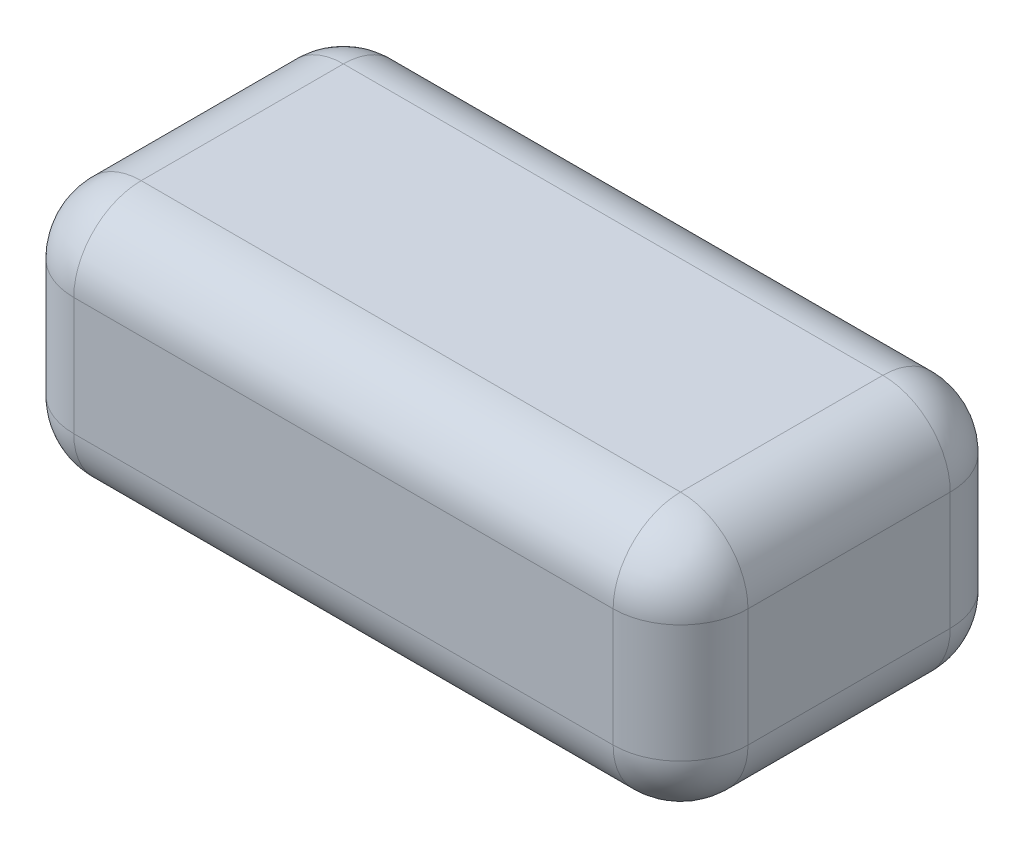
SolidWorks part; units mm, degrees
ref_plane "Front Plane" through (0, 0, 0) normal (0, 0, 1) x (1, 0, 0)
ref_plane "Top Plane" through (0, 0, 0) normal (0, 1, 0) x (1, 0, 0)
ref_plane "Right Plane" through (0, 0, 0) normal (1, 0, 0) x (0, 0, -1)
sketch "Sketch1" plane through (0, 0, 0) normal (0, 1, 0) x (1, 0, 0)
  line L1 (-100, -50) -> (100, -50)
  line L2 (-100, -50) -> (-100, 50)
  line L3 (-100, 50) -> (100, 50)
  line L4 (100, -50) -> (100, 50)
  line L5 (-100, -50) -> (100, 50) construction
  line L6 (-100, 50) -> (100, -50) construction
  point P0 (0, 0)
  dimension "D1" = 100
  dimension "D2" = 200
extrude "Boss-Extrude1" add sketch "Sketch1" along normal blind 75
fillet "Fillet1" radius 20 12 edges at (-100, 0, 0) (-100, 37.5, -50) (0, 0, -50) (0, 75, -50) (100, 37.5, -50) (100, 0, 0) (100, 75, 0) (0, 0, 50) (100, 37.5, 50) (0, 75, 50) (-100, 75, 0) (-100, 37.5, 50)
